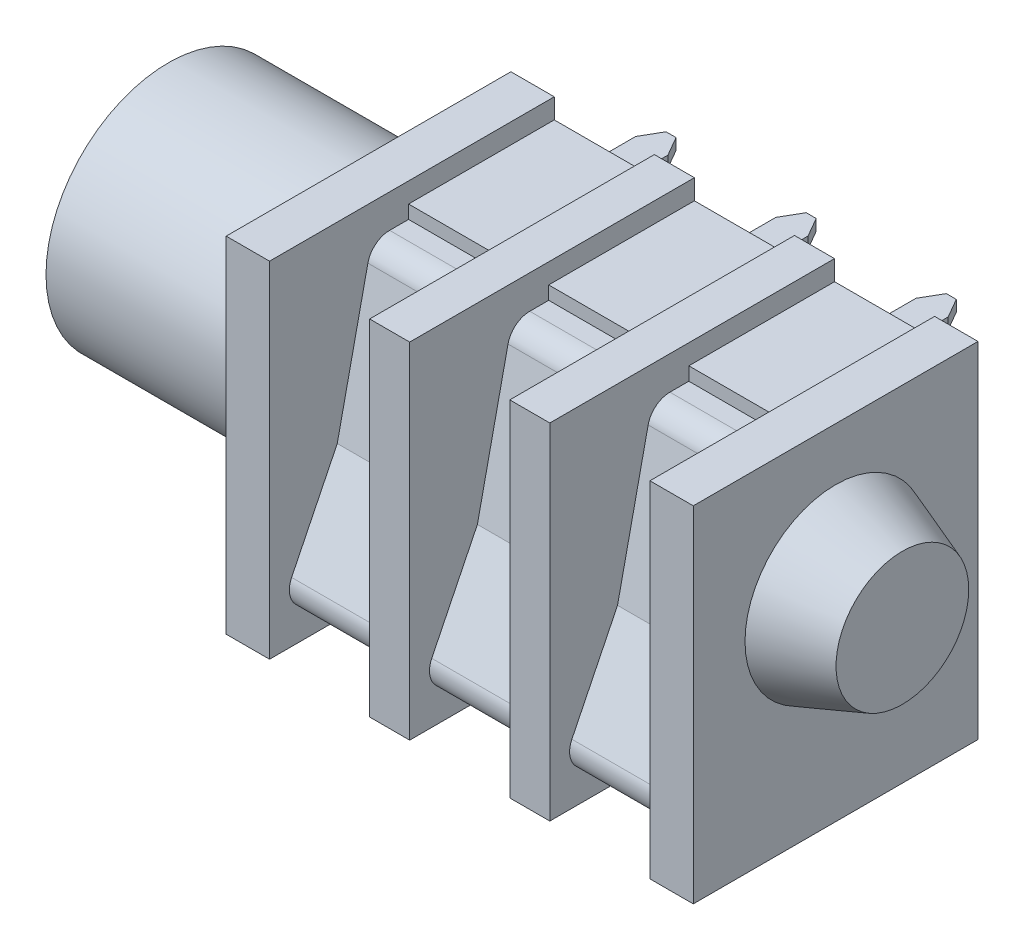
SolidWorks part; units mm, degrees
ref_plane "Front Plane" through (0, 0, 0) normal (0, 0, 1) x (1, 0, 0)
ref_plane "Top Plane" through (0, 0, 0) normal (0, 1, 0) x (1, 0, 0)
ref_plane "Right Plane" through (0, 0, 0) normal (1, 0, 0) x (0, 0, -1)
sketch "Sketch1" plane through (0, 0, 0) normal (1, 0, 0) x (0, 0, -1)
  line L1 (0, 0) -> (12.8, 0)
  line L2 (0, 0) -> (0, 15.5)
  line L3 (0, 15.5) -> (12.8, 15.5)
  line L4 (12.8, 0) -> (12.8, 15.5)
  dimension "D1" = 15.5
  dimension "D2" = 12.8
extrude "Boss-Extrude1" add sketch "Sketch1" along normal blind 21
sketch "Sketch2" plane through (0, 0, 0) normal (-1, 0, 0) x (0, 0, 1)
  line L0 (-6.4, 15.5) -> (-6.4, 0) construction
  line L1 (-12.8, 15.5) -> (0, 15.5) construction
  line L2 (0, 0) -> (-12.8, 0) construction
  line L3 (-12.8, 9.05) -> (0, 9.05) construction
  line L4 (-12.8, 0) -> (-12.8, 15.5) construction
  line L5 (-12.8, 7.75) -> (0, 7.75) construction
  line L6 (0, 15.5) -> (0, 0) construction
  circle A0 centre (-6.4, 9.05) radius 3.2
  circle A1 centre (-6.4, 9.05) radius 5.5
  dimension "D2" = 6.4
  dimension "D3" = 11
  dimension "D1" = 1.3
extrude "Boss-Extrude2" add sketch "Sketch2" along normal blind 9
sketch "Sketch3" plane through (21, 0, 0) normal (1, 0, 0) x (0, 0, -1)
  line L0 (6.4, 15.5) -> (6.4, 0) construction
  line L1 (12.8, 15.5) -> (0, 15.5) construction
  line L2 (0, 0) -> (12.8, 0) construction
  line L4 (0, 15.5) -> (0, 0) construction
  line L5 (0, 7.75) -> (12.8, 7.75) construction
  line L6 (12.8, 0) -> (12.8, 15.5) construction
  line L8 (12.8, 9.05) -> (0, 9.05) construction
  circle A0 centre (6.4, 9.05) radius 4.075
  dimension "D2" = 8.15
  dimension "D1" = 1.3
extrude "Boss-Extrude3" add sketch "Sketch3" along normal blind 3 draft 20
ref_plane "Plane1" through (4.2, 0, 0) normal (-1, 0, 0) x (0, 0, 1)
sketch "Sketch6" plane through (0, 0, 0) normal (0, -1, 0) x (1, 0, 0)
  line L0 (21, 0) -> (0, 0) construction
  line L1 (1.95, 0) -> (6.45, 0)
  line L2 (1.95, 0) -> (1.95, -6.25)
  line L3 (1.95, -6.25) -> (6.45, -6.25)
  line L4 (6.45, 0) -> (6.45, -6.25)
  line L5 (4.2, 7.04) -> (4.2, -7.04) construction
  point P6 (4.2, -6.25)
  dimension "D1" = 6.25
  dimension "D2" = 4.5
extrude "Cut-Extrude1" cut sketch "Sketch6" against normal up to next (15.5 mm away)
sketch "Sketch7" plane through (0, 0, -12.8) normal (0, 0, -1) x (-1, 0, 0)
  line L0 (-1.95, 15.5) -> (-1.95, 0) construction
  line L1 (-6.45, 15.5) -> (-1.95, 15.5)
  line L2 (-6.45, 15.5) -> (-6.45, 14.6)
  line L3 (-6.45, 14.6) -> (-1.95, 14.6)
  line L4 (-1.95, 15.5) -> (-1.95, 14.6)
  line L6 (-6.45, 0) -> (-1.95, 0)
  line L7 (-6.45, 0) -> (-6.45, 0.9)
  line L8 (-6.45, 0.9) -> (-1.95, 0.9)
  line L9 (-1.95, 0) -> (-1.95, 0.9)
  dimension "D1" = 0.9
  dimension "D2" = 0.9
extrude "Cut-Extrude2" cut sketch "Sketch7" against normal blind 9
pattern_linear "LPattern1" count 3 spacing 6.3 along (1, 0, 0) of "Cut-Extrude1", "Cut-Extrude2"
sketch "Sketch8" plane through (4.2, 0, 0) normal (-1, 0, 0) x (0, 0, 1)
  line L1 (-6.25, 13.5) -> (-5.3982, 13.5)
  line L2 (-6.25, 14.6) -> (-6.25, 0.9) construction
  line L3 (-6.25, 1.75) -> (-1.89, 1.75)
  line L4 (-1.441, 2.4701) -> (-3.52, 6.7107)
  line L5 (-3.52, 6.7107) -> (-4.9096, 13.1062)
  line L6 (0, 0) -> (-12.8, 0) construction
  line L7 (-12.8, 15.5) -> (0, 15.5) construction
  arc A1 (-1.441, 2.4701) -> (-1.89, 1.75) centre (-1.89, 2.25) cw
  arc A2 (-5.3982, 13.5) -> (-4.9096, 13.1062) centre (-5.3982, 13) cw
  dimension "D1" = 0.5
  dimension "D4" = 0.5
  dimension "D2" = 1.75
  dimension "D3" = 2
extrude "Extrude-Thin1" add sketch "Sketch8" along normal mid plane 4.5 thin thin type one direction wall 0.5
sketch "Sketch9" plane through (4.2, 0, 0) normal (-1, 0, 0) x (0, 0, 1)
  line L0 (-12.8, 13.4) -> (-15.8, 13.4)
  line L1 (-12.8, 0) -> (-12.8, 15.5) construction
  line L2 (-12.8, 2.1) -> (-15.8, 2.1)
  line L5 (0, 7.75) -> (-25.5672, 7.75) construction
  line L6 (0, 15.5) -> (0, 0) construction
  line L7 (-15.8, 13.4) -> (-15.8, 2.1) construction
  point P8 (-15.8, 7.75)
  dimension "D1" = 3
  dimension "D2" = 11.3
extrude "Extrude-Thin2" add sketch "Sketch9" along normal mid plane 1.45 thin thin type mid plane wall 0.5
chamfer "Chamfer1" distance 0.5 angle 60 4 edges at (4.925, 2.1, -15.8) (4.925, 13.4, -15.8) (3.475, 2.1, -15.8) (3.475, 13.4, -15.8)
pattern_linear "LPattern2" count 3 spacing 6.3 along (1, 0, 0) of "Extrude-Thin1", "Extrude-Thin2", "Chamfer1"
